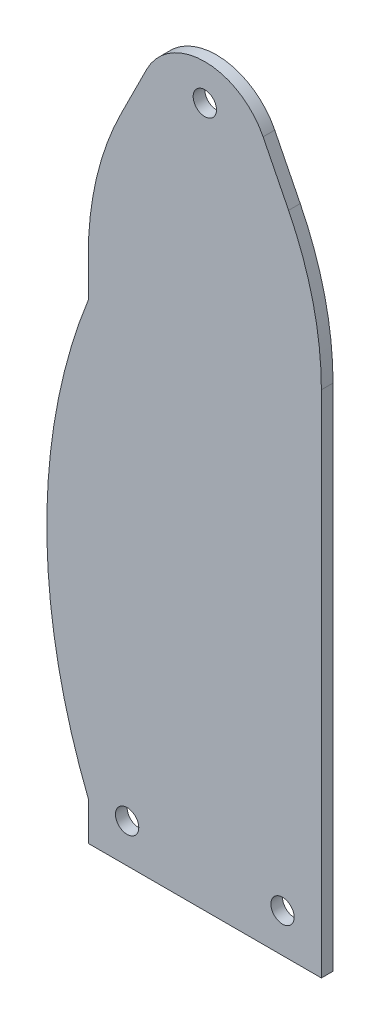
SolidWorks part; units mm, degrees
material "普通碳钢"
ref_plane "前视基准面" through (0, 0, 0) normal (0, 0, 1) x (1, 0, 0)
ref_plane "上视基准面" through (0, 0, 0) normal (0, 1, 0) x (1, 0, 0)
ref_plane "右视基准面" through (0, 0, 0) normal (1, 0, 0) x (0, 0, -1)
sketch "草图1" plane through (0, 0, 0) normal (0, 0, 1) x (1, 0, 0)
  line L0 (8.4458, 166.8916) -> (15, 180)
  line L1 (30, 180) -> (30, 0) construction
  line L2 (15, 180) -> (45, 180) construction
  line L3 (0, 131.1146) -> (0, 121.1146)
  line L4 (0, 0) -> (60, 0)
  line L5 (60, 131.1146) -> (60, 0)
  line L6 (51.5542, 166.8916) -> (45, 180)
  line L7 (0, 10) -> (0, 0)
  arc A0 (60, 131.1146) -> (51.5542, 166.8916) centre (-20, 131.1146) ccw
  arc A1 (0, 131.1146) -> (8.4458, 166.8916) centre (80, 131.1146) cw
  arc A2 (15, 180) -> (45, 180) centre (30, 172.5) cw
  circle A3 centre (50, 10) radius 3
  circle A4 centre (30, 180) radius 3
  circle A5 centre (10, 10) radius 3
  arc A6 (0, 10) -> (0, 121.1146) centre (139.3319, 65.5573) cw
  point P13 (60, 150)
  point P16 (0, 150)
  dimension "D5" = 80
  dimension "D6" = 80
  dimension "D7" = 6
  dimension "D8" = 10
  dimension "D10" = 150
  dimension "D12" = 6
  dimension "D9" = 10
  dimension "D1" = 30
  dimension "D2" = 60
  dimension "D3" = 15
  dimension "D4" = 180
  dimension "D13" = 10
  dimension "D14" = 10
extrude "凸台-拉伸1" add sketch "草图1" along normal blind 3
